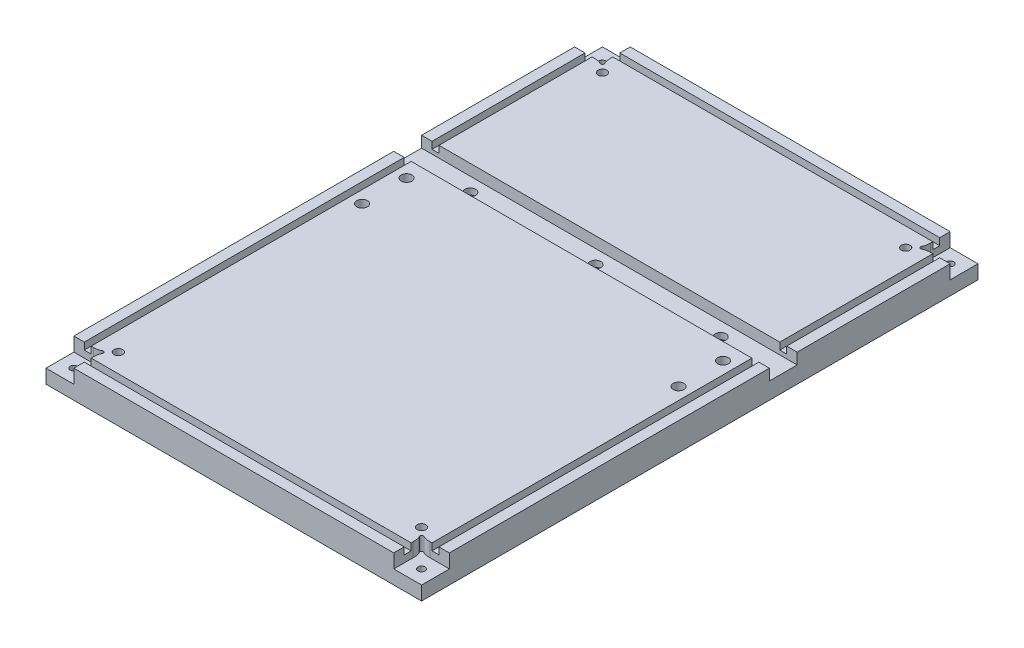
SolidWorks part; units mm, degrees
ref_plane "Front Plane" through (0, 0, 0) normal (0, 0, 1) x (1, 0, 0)
ref_plane "Top Plane" through (0, 0, 0) normal (0, 1, 0) x (1, 0, 0)
ref_plane "Right Plane" through (0, 0, 0) normal (1, 0, 0) x (0, 0, -1)
sketch "Base" plane through (0, 0, 0) normal (0, 1, 0) x (1, 0, 0)
  line L1 (-201.9764, 133.7508) -> (140.9236, 133.7508)
  line L2 (-201.9764, 133.7508) -> (-201.9764, -374.2492)
  line L3 (-201.9764, -374.2492) -> (140.9236, -374.2492)
  line L4 (140.9236, 133.7508) -> (140.9236, -374.2492)
  dimension "D1" = 342.9
  dimension "D2" = 508
extrude "Boss-Extrude1" add sketch "Base" along normal blind 25.4
sketch "Sketch2" plane through (0, 25.4, 0) normal (0, 1, 0) x (1, 0, 0)
  line L1 (172.6736, -31.3492) -> (-233.7264, -31.3492)
  line L2 (172.6736, -31.3492) -> (172.6736, -56.7492)
  line L3 (172.6736, -56.7492) -> (-233.7264, -56.7492)
  line L4 (-233.7264, -31.3492) -> (-233.7264, -56.7492)
  line L6 (140.9236, 133.7508) -> (-201.9764, 133.7508) construction
  line L9 (-30.5264, 133.7508) -> (-30.5264, -374.2492) construction
  line L10 (-201.9764, -374.2492) -> (140.9236, -374.2492) construction
  point P6 (-30.5264, -31.3492)
  dimension "D1" = 317.5
  dimension "D2" = 25.4
  dimension "D3" = 406.4
extrude "Cut-Extrude1" cut sketch "Sketch2" against normal blind 10.16
hole_wizard "CBORE for 3/8 Socket Head Cap Screw4" positions "3DSketch1" profile "Sketch3" counterbore size "3/8" standard "ANSI Inch" end condition up to next
sketch3d "3DSketch1"
  line L3 (-201.9764, 0, -133.7508) -> (-201.9764, 0, 374.2492) construction
  point P0 (83.7736, 0, 44.0492)
  point P2 (-30.5264, 0, 44.0492)
  point P4 (-144.8264, 0, 44.0492)
  dimension "D1" = 12.7
  dimension "D2" = 12.7
  dimension "D3" = 12.7
  dimension "D4" = 171.45
  dimension "D5" = 114.3
  dimension "D6" = 114.3
sketch "Sketch3" plane through (83.7736, 0, 44.0492) normal (1, 0, 0) x (0, 0, -1)
  line L0 (0, 0) -> (0, 15.24)
  line L1 (0, 15.24) -> (4.9022, 15.24)
  line L3 (4.9022, 15.24) -> (4.9022, 9.525)
  line L4 (4.9022, 9.525) -> (7.9375, 9.525)
  line L5 (7.9375, 9.525) -> (7.9375, 0)
  line L7 (7.9375, 0) -> (0, 0)
  line L11 (0, -6.35) -> (0, 107.95) construction
  dimension "Thru Hole Dia." = 9.8044
  dimension "Thru Hole Depth" = 15.24
  dimension "C'Bore Dia." = 15.875
  dimension "C'Bore Depth" = 9.525
hole_wizard "CBORE for 3/8 Socket Head Cap Screw3" positions "Sketch4" profile "Sketch6" counterbore size "3/8" standard "ANSI Inch" end condition up to next
sketch "Sketch4" plane through (0, 0, 0) normal (0, -1, 0) x (-1, 0, 0)
  line L0 (201.9764, -56.7492) -> (-140.9236, -56.7492) construction
  line L1 (-140.9236, -374.2492) -> (-140.9236, 133.7508) construction
  line L3 (201.9764, 133.7508) -> (201.9764, -374.2492) construction
  point P0 (-113.9361, -71.9892)
  point P2 (-113.9361, -112.6292)
  point P4 (174.9889, -71.9892)
  point P6 (174.9889, -112.6292)
  dimension "D1" = 15.24
  dimension "D2" = 26.9875
  dimension "D3" = 26.9875
  dimension "D4" = 40.64
  dimension "D5" = 15.24
  dimension "D6" = 26.9875
  dimension "D7" = 40.64
  dimension "D8" = 26.9875
sketch "Sketch6" plane through (113.9361, 0, 71.9892) normal (1, 0, 0) x (0, 0, -1)
  line L0 (0, 0) -> (0, 25.4)
  line L1 (0, 25.4) -> (4.9022, 25.4)
  line L3 (4.9022, 25.4) -> (4.9022, 15.24)
  line L4 (4.9022, 15.24) -> (7.9375, 15.24)
  line L5 (7.9375, 15.24) -> (7.9375, 0)
  line L7 (7.9375, 0) -> (0, 0)
  line L11 (0, -6.35) -> (0, 107.95) construction
  dimension "Thru Hole Dia." = 9.8044
  dimension "Thru Hole Depth" = 25.4
  dimension "C'Bore Dia." = 15.875
  dimension "C'Bore Depth" = 15.24
hole_wizard "CBORE for 1/4 Socket Head Cap Screw1" positions "3DSketch2" profile "Sketch9" counterbore size "1/4" standard "ANSI Inch" end condition up to next
sketch3d "3DSketch2"
  line L0 (140.9236, 0, -133.7508) -> (-201.9764, 0, -133.7508) construction
  line L1 (140.9236, 0, 374.2492) -> (140.9236, 0, -133.7508) construction
  line L2 (-201.9764, 0, -133.7508) -> (-201.9764, 0, 374.2492) construction
  line L3 (-201.9764, 0, 374.2492) -> (140.9236, 0, 374.2492) construction
  point P0 (128.2236, 0, 361.5492)
  point P2 (-189.2764, 0, 361.5492)
  point P4 (-189.2764, 0, -121.0508)
  point P6 (128.2236, 0, -121.0508)
  dimension "D1" = 12.7
  dimension "D2" = 12.7
  dimension "D3" = 12.7
  dimension "D4" = 12.7
  dimension "D5" = 12.7
  dimension "D6" = 12.7
  dimension "D7" = 12.7
  dimension "D8" = 12.7
sketch "Sketch9" plane through (128.2236, 0, 361.5492) normal (1, 0, 0) x (0, 0, -1)
  line L0 (0, 0) -> (0, 25.4)
  line L1 (0, 25.4) -> (3.2639, 25.4)
  line L3 (3.2639, 25.4) -> (3.2639, 6.35)
  line L4 (3.2639, 6.35) -> (5.5562, 6.35)
  line L5 (5.5562, 6.35) -> (5.5562, 0)
  line L7 (5.5562, 0) -> (0, 0)
  line L11 (0, -6.35) -> (0, 107.95) construction
  dimension "Thru Hole Dia." = 6.5278
  dimension "Thru Hole Depth" = 25.4
  dimension "C'Bore Dia." = 11.1125
  dimension "C'Bore Depth" = 6.35
sketch "Sketch8" plane through (0, 25.4, 0) normal (0, 1, 0) x (1, 0, 0)
  line L0 (116.3173, -347.4744) -> (115.5236, -348.8492) construction
  line L1 (140.9236, -374.2492) -> (115.5236, -374.2492)
  line L2 (140.9236, -374.2492) -> (140.9236, -348.8492)
  line L3 (140.9236, -348.8492) -> (123.1436, -348.8492)
  line L4 (115.5236, -374.2492) -> (115.5236, -356.4692)
  line L5 (-201.9764, -374.2492) -> (-176.5764, -374.2492)
  line L6 (-201.9764, -374.2492) -> (-201.9764, -348.8492)
  line L7 (-201.9764, -348.8492) -> (-184.1964, -348.8492)
  line L8 (-176.5764, -374.2492) -> (-176.5764, -356.4692)
  line L9 (-201.9764, 133.7508) -> (-176.5764, 133.7508)
  line L10 (-201.9764, 133.7508) -> (-201.9764, 108.3508)
  line L11 (-201.9764, 108.3508) -> (-184.1964, 108.3508)
  line L12 (-176.5764, 133.7508) -> (-176.5764, 115.9708)
  line L13 (140.9236, 133.7508) -> (115.5236, 133.7508)
  line L14 (140.9236, 133.7508) -> (140.9236, 108.3508)
  line L15 (140.9236, 108.3508) -> (123.1436, 108.3508)
  line L16 (115.5236, 133.7508) -> (115.5236, 115.9708)
  line L17 (115.5236, -348.8492) -> (123.1436, -348.8492) construction
  line L18 (115.5236, -356.4692) -> (115.5236, -348.8492) construction
  line L19 (115.5236, -348.8492) -> (114.1488, -349.6429) construction
  line L20 (115.5236, 108.3508) -> (116.3173, 106.976) construction
  line L21 (115.5236, 108.3508) -> (114.1488, 109.1446) construction
  line L22 (-176.5764, 108.3508) -> (-175.2016, 109.1446) construction
  line L23 (-176.5764, 108.3508) -> (-177.3702, 106.976) construction
  line L24 (-176.5764, -348.8492) -> (-175.2016, -349.6429) construction
  line L25 (-176.5764, -348.8492) -> (-177.3702, -347.4744) construction
  arc A0 (116.3173, -347.4744) -> (114.1488, -349.6429) centre (115.5236, -348.8492) ccw
  arc A1 (114.1488, 109.1446) -> (116.3173, 106.976) centre (115.5236, 108.3508) ccw
  arc A2 (-177.3702, 106.976) -> (-175.2016, 109.1446) centre (-176.5764, 108.3508) ccw
  arc A3 (-175.2016, -349.6429) -> (-177.3702, -347.4744) centre (-176.5764, -348.8492) ccw
  spline S0 degree 3 poles (123.1436, -348.8492) (120.8225, -348.8492) (118.3275, -348.6349) (116.3173, -347.4744) knots 0 0 0 0 1 1 1 1
  spline S1 degree 3 poles (115.5236, -356.4692) (115.5236, -353.9168) (115.3093, -351.6531) (114.1488, -349.6429) knots 0 0 0 0 1 1 1 1
  spline S2 degree 3 poles (123.1436, 108.3508) (120.8225, 108.3508) (118.3275, 108.1366) (116.3173, 106.976) knots 0 0 0 0 1 1 1 1
  spline S3 degree 3 poles (114.1488, 109.1446) (115.3093, 111.1547) (115.5236, 113.6497) (115.5236, 115.9708) knots 0 0 0 0 1 1 1 1
  spline S4 degree 3 poles (-176.5764, 115.9708) (-176.5764, 113.4184) (-176.3621, 111.1547) (-175.2016, 109.1446) knots 0 0 0 0 1 1 1 1
  spline S5 degree 3 poles (-177.3702, 106.976) (-179.3803, 108.1366) (-181.8753, 108.3508) (-184.1964, 108.3508) knots 0 0 0 0 1 1 1 1
  spline S6 degree 3 poles (-175.2016, -349.6429) (-176.7942, -352.4013) (-176.5764, -354.9687) (-176.5764, -356.4692) knots 0 0 0 0 1 1 1 1
  spline S7 degree 3 poles (-177.3702, -347.4744) (-180.1285, -349.0669) (-182.696, -348.8492) (-184.1964, -348.8492) knots 0 0 0 0 1 1 1 1
  point P23 (117.1111, -348.8492)
  point P27 (115.5236, -350.4367)
  dimension "D9" = 7.62
  dimension "D10" = 1.5875
  dimension "D15" = 60
  dimension "D16" = 1.5875
  dimension "D20" = 3.175
  dimension "D25" = 60
  dimension "D28" = 3.175
  dimension "D2" = 25.4
  dimension "D3" = 25.4
  dimension "D4" = 25.4
  dimension "D5" = 25.4
  dimension "D6" = 25.4
  dimension "D7" = 25.4
  dimension "D8" = 25.4
  dimension "D11" = 7.62
  dimension "D12" = 25.4
  dimension "D13" = 60
  dimension "D14" = 60
  dimension "D17" = 60
  dimension "D18" = 7.62
  dimension "D19" = 7.62
  dimension "D21" = 60
  dimension "D22" = 60
  dimension "D23" = 7.62
  dimension "D24" = 7.62
  dimension "D26" = 60
  dimension "D27" = 7.62
  dimension "D29" = 7.62
extrude "Cut-Extrude3" cut sketch "Sketch8" against normal blind 12.7
sketch "Sketch10" plane through (0, 25.4, 0) normal (0, 1, 0) x (1, 0, 0)
  line L1 (125.0486, 108.3508) -> (131.3986, 108.3508)
  line L2 (125.0486, 108.3508) -> (125.0486, -348.8492)
  line L3 (125.0486, -348.8492) -> (131.3986, -348.8492)
  line L4 (131.3986, 108.3508) -> (131.3986, -348.8492)
  line L5 (140.9236, -348.8492) -> (140.9236, -56.7492) construction
  line L8 (-201.9764, 108.3508) -> (-201.9764, -31.3492) construction
  line L9 (-192.4514, 108.3508) -> (-186.1014, 108.3508)
  line L10 (-192.4514, 108.3508) -> (-192.4514, -348.8492)
  line L11 (-192.4514, -348.8492) -> (-186.1014, -348.8492)
  line L12 (-186.1014, 108.3508) -> (-186.1014, -348.8492)
  line L13 (-184.1964, -348.8492) -> (-201.9764, -348.8492) construction
  line L14 (-201.9764, 108.3508) -> (-184.1964, 108.3508) construction
  line L15 (123.1436, 108.3508) -> (140.9236, 108.3508) construction
  line L16 (140.9236, -348.8492) -> (123.1436, -348.8492) construction
  line L17 (-176.5764, 115.9708) -> (-176.5764, 133.7508) construction
  line L18 (-176.5764, 124.2258) -> (115.5236, 124.2258)
  line L19 (-176.5764, 124.2258) -> (-176.5764, 117.8758)
  line L20 (-176.5764, 117.8758) -> (115.5236, 117.8758)
  line L21 (115.5236, 124.2258) -> (115.5236, 117.8758)
  line L22 (115.5236, 133.7508) -> (115.5236, 115.9708) construction
  line L23 (115.5236, 133.7508) -> (-176.5764, 133.7508) construction
  line L24 (-176.5764, -374.2492) -> (-176.5764, -356.4692) construction
  line L25 (-176.5764, -358.3742) -> (115.5236, -358.3742)
  line L26 (-176.5764, -358.3742) -> (-176.5764, -364.7242)
  line L27 (-176.5764, -364.7242) -> (115.5236, -364.7242)
  line L28 (115.5236, -358.3742) -> (115.5236, -364.7242)
  line L29 (115.5236, -356.4692) -> (115.5236, -374.2492) construction
  line L30 (-176.5764, -374.2492) -> (115.5236, -374.2492) construction
  dimension "D1" = 6.35
  dimension "D2" = 6.35
  dimension "D3" = 9.525
  dimension "D4" = 9.525
  dimension "D5" = 6.35
  dimension "D6" = 9.525
  dimension "D7" = 9.525
  dimension "D8" = 6.35
extrude "Cut-Extrude4" cut sketch "Sketch10" against normal blind 6.35
hole_wizard "3/8-16 Tapped Hole2" positions "Sketch17" profile "Sketch18" tap size "3/8-16" standard "ANSI Inch" end condition up to next
sketch "Sketch17" plane through (0, 0, 0) normal (0, -1, 0) x (-1, 0, 0)
  line L0 (-140.9236, 133.7508) -> (201.9764, 133.7508) construction
  line L1 (-140.9236, -374.2492) -> (-140.9236, 133.7508) construction
  line L2 (201.9764, 133.7508) -> (201.9764, -374.2492) construction
  line L3 (201.9764, -374.2492) -> (-140.9236, -374.2492) construction
  point P0 (-107.9036, -341.2292)
  point P2 (168.9564, -341.2292)
  point P4 (168.9564, 100.7308)
  point P6 (-107.9036, 100.7308)
  dimension "D1" = 33.02
  dimension "D2" = 33.02
  dimension "D3" = 33.02
  dimension "D4" = 33.02
  dimension "D5" = 33.02
  dimension "D6" = 33.02
  dimension "D7" = 33.02
  dimension "D8" = 33.02
sketch "Sketch18" plane through (107.9036, 0, 341.2292) normal (1, 0, 0) x (0, 0, -1)
  line L0 (0, 0) -> (0, 25.4)
  line L1 (0, 25.4) -> (3.9687, 25.4)
  line L2 (3.9687, 25.4) -> (3.9687, 0)
  line L5 (3.9687, 0) -> (0, 0)
  line L11 (0, -6.35) -> (0, 107.95) construction
  dimension "Thru Tap Drill Dia." = 7.9375
  dimension "Thru Tap Drill Depth" = 25.4
cosmetic thread "Hole Thread5" parameters "D2"=9.525
cosmetic thread "Hole Thread6" parameters "D2"=9.525
cosmetic thread "Hole Thread7" parameters "D2"=9.525
cosmetic thread "Hole Thread8" parameters "D2"=9.525
sketch "Sketch19" plane through (0, 0, 0) normal (0, -1, 0) x (1, 0, 0)
  circle A0 centre (-168.9564, -100.7308) radius 9.525
  circle A1 centre (-168.9564, 341.2292) radius 9.525
  circle A2 centre (107.9036, 341.2292) radius 9.525
  circle A3 centre (108.2173, -100.7308) radius 9.525
  dimension "D1" = 19.05
  dimension "D2" = 19.05
  dimension "D3" = 19.05
  dimension "D4" = 19.05
extrude "Cut-Extrude5" cut sketch "Sketch19" against normal blind 1.27
